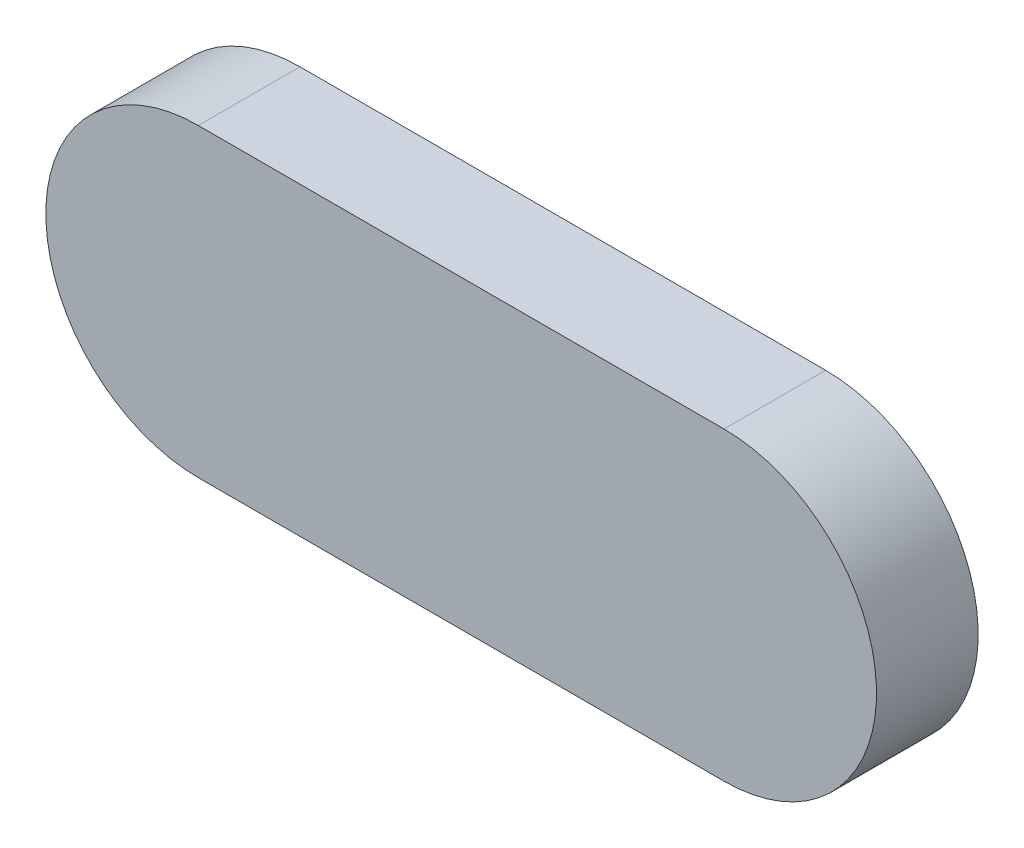
SolidWorks part; units mm, degrees
ref_plane "前视基准面" through (0, 0, 0) normal (0, 0, 1) x (1, 0, 0)
ref_plane "上视基准面" through (0, 0, 0) normal (0, 1, 0) x (1, 0, 0)
ref_plane "右视基准面" through (0, 0, 0) normal (1, 0, 0) x (0, 0, -1)
sketch "草图1" plane through (0, 0, 0) normal (0, 0, 1) x (1, 0, 0)
  line L1 (12.925, 7.5) -> (-12.925, 7.5)
  line L2 (12.925, 7.5) -> (12.925, -7.5) construction
  line L3 (12.925, -7.5) -> (-12.925, -7.5)
  line L4 (-12.925, 7.5) -> (-12.925, -7.5) construction
  line L5 (12.925, 7.5) -> (-12.925, -7.5) construction
  line L6 (12.925, -7.5) -> (-12.925, 7.5) construction
  line L7 (22.925, -10) -> (-22.925, -10) construction
  line L8 (22.925, -10) -> (22.925, 10) construction
  line L9 (22.925, 10) -> (-22.925, 10) construction
  line L10 (-22.925, -10) -> (-22.925, 10) construction
  line L11 (22.925, -10) -> (-22.925, 10) construction
  line L12 (22.925, 10) -> (-22.925, -10) construction
  arc A0 (12.925, 7.5) -> (12.925, -7.5) centre (12.925, 0) cw
  arc A1 (-12.925, 7.5) -> (-12.925, -7.5) centre (-12.925, 0) ccw
  point P0 (0, 0)
  point P8 (0, 0)
  point P13 (20.425, 0)
  dimension "D1" = 20
  dimension "D2" = 2.5
  dimension "D3" = 2.5
  dimension "D4" = 45.85
extrude "凸台-拉伸1" add sketch "草图1" along normal mid plane 5
